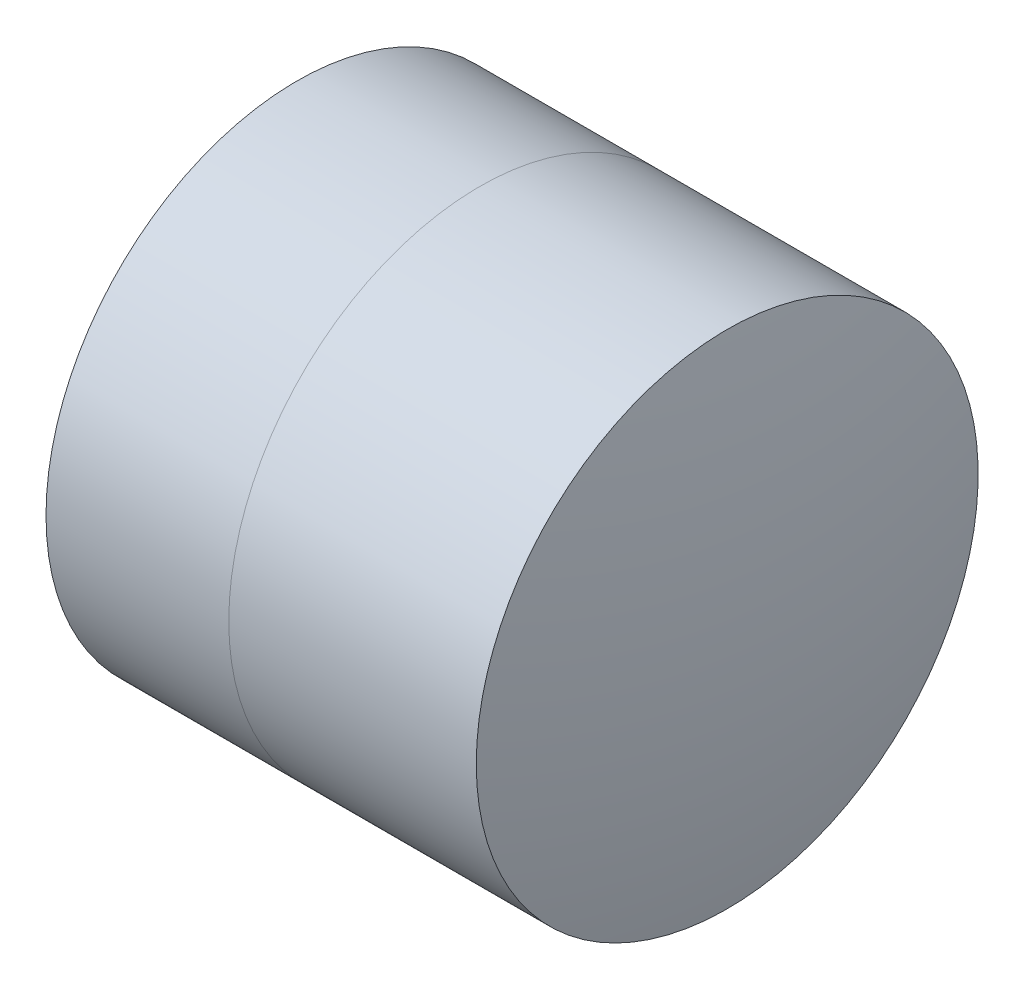
SolidWorks part; units mm, degrees
ref_plane "前视基准面" through (0, 0, 0) normal (0, 0, 1) x (1, 0, 0)
ref_plane "上视基准面" through (0, 0, 0) normal (0, 1, 0) x (1, 0, 0)
ref_plane "右视基准面" through (0, 0, 0) normal (1, 0, 0) x (0, 0, -1)
sketch "草图1" plane through (0, 0, 0) normal (0, 1, 0) x (1, 0, 0)
  line L0 (-0.8161, 0) -> (5.2377, 0) construction
  line L1 (2.2476, -2.5) -> (4.0684, -2.5)
  line L2 (2.2476, 2.5) -> (4.0684, 2.5)
  arc A0 (4.0684, -2.5) -> (4.0684, 2.5) centre (-0.605, 0) ccw
  arc A1 (2.2476, 2.5) -> (2.2476, -2.5) centre (14.495, 0) ccw
  point P10 (1.995, 0)
  point P11 (4.695, 0)
  dimension "D3" = 12.5
  dimension "D4" = 5.3
  dimension "D1" = 2.5
  dimension "D2" = 2.5
  dimension "D5" = 2.7
revolve "旋转1" add sketch "草图1" angle 360 about L0
sketch "草图2" plane through (0, 0, 0) normal (0, 1, 0) x (1, 0, 0)
  line L0 (-0.5519, 0) -> (7.349, 0) construction
  line L2 (4.0684, 2.5) -> (6.534, 2.5)
  line L3 (4.0684, -2.5) -> (6.534, -2.5)
  arc A0 (6.534, -2.5) -> (6.534, 2.5) centre (-5.305, 0) ccw
  arc A1 (4.0684, -2.5) -> (4.0684, 2.5) centre (-0.605, 0) ccw construction
  arc A2 (4.0684, -2.5) -> (4.0684, 2.5) centre (-0.605, 0) ccw
  point P4 (4.695, 0)
  point P8 (6.795, 0)
  point P9 (7.349, 0)
  dimension "D1" = 12.1
  dimension "D2" = 2.1
revolve "旋转3" add sketch "草图2" angle 360 about L0
